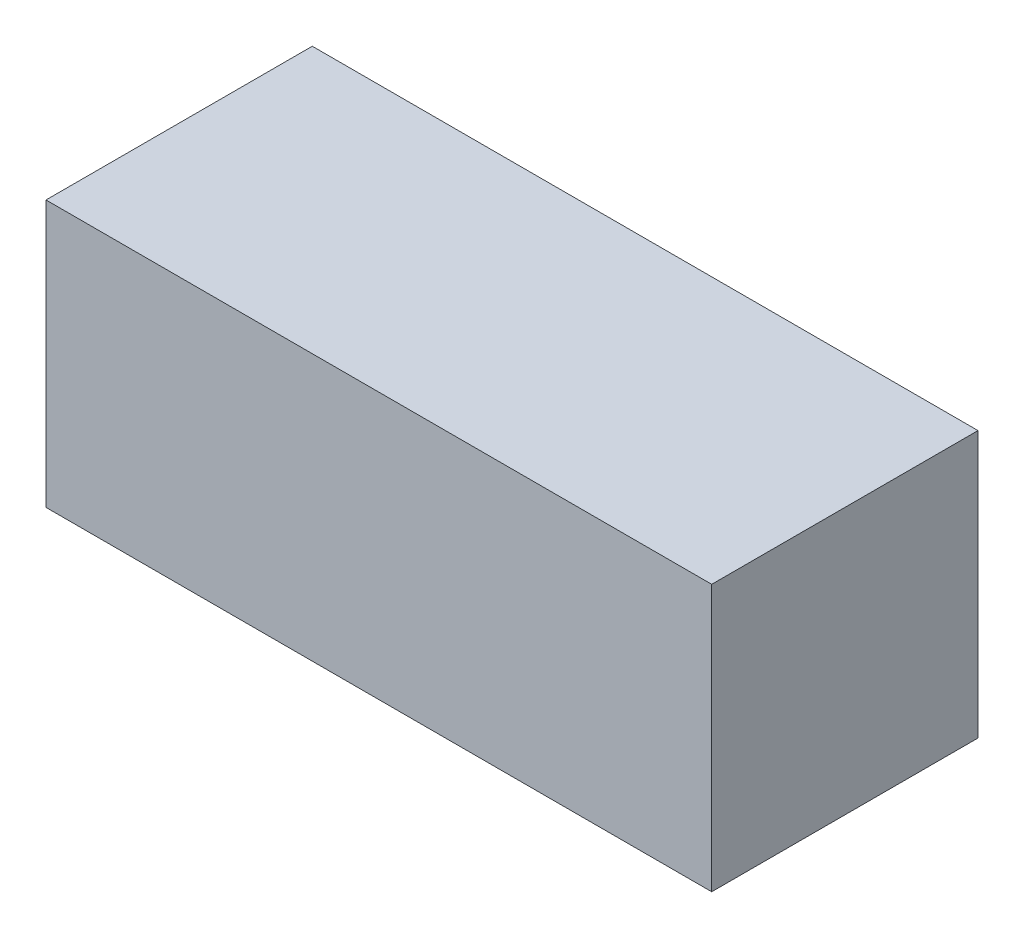
SolidWorks part; units mm, degrees
material "Nylon 6/10"
ref_plane "Front Plane" through (0, 0, 0) normal (0, 0, 1) x (1, 0, 0)
ref_plane "Top Plane" through (0, 0, 0) normal (0, 1, 0) x (1, 0, 0)
ref_plane "Right Plane" through (0, 0, 0) normal (1, 0, 0) x (0, 0, -1)
sketch "Sketch1" plane through (0, 0, 0) normal (1, 0, 0) x (0, 0, -1)
  line L1 (-50.8, -50.8) -> (50.8, -50.8)
  line L2 (-50.8, -50.8) -> (-50.8, 50.8)
  line L3 (-50.8, 50.8) -> (50.8, 50.8)
  line L4 (50.8, -50.8) -> (50.8, 50.8)
  line L5 (-50.8, -50.8) -> (50.8, 50.8) construction
  line L6 (-50.8, 50.8) -> (50.8, -50.8) construction
  point P0 (0, 0)
  dimension "D1" = 101.6
  dimension "D2" = 101.6
extrude "Boss-Extrude1" add sketch "Sketch1" along normal blind 254 contours L3 L4 L1 L2
